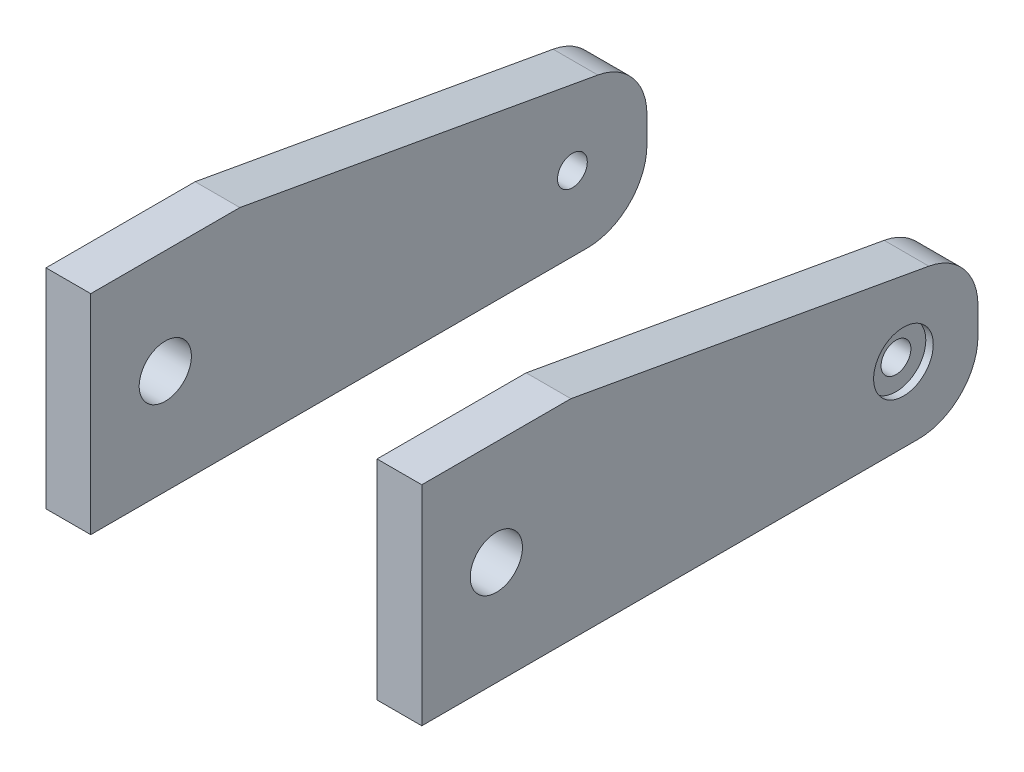
SolidWorks part; units mm, degrees
ref_plane "Front Plane" through (0, 0, 0) normal (0, 0, 1) x (1, 0, 0)
ref_plane "Top Plane" through (0, 0, 0) normal (0, 1, 0) x (1, 0, 0)
ref_plane "Right Plane" through (0, 0, 0) normal (1, 0, 0) x (0, 0, -1)
sketch "Sketch2" plane through (9.6, 0, 0) normal (1, 0, 0) x (0, 0, -1)
  line L0 (-22.3234, -11) -> (0.9766, -11)
  line L1 (4.9766, -7) -> (4.9766, -5.2432)
  line L2 (1.6828, -1.306) -> (-22.3234, 3)
  line L3 (-22.3234, 3) -> (-22.3234, -11) construction
  line L4 (-9.6234, -7.3) -> (-9.6234, 0) construction
  line L5 (-22.3234, -11) -> (-32.3234, -11)
  line L6 (-32.3234, -11) -> (-32.3234, 3)
  line L7 (-32.3234, 3) -> (-22.3234, 3)
  line L8 (-32.3234, -11) -> (-22.3234, 3) construction
  circle A0 centre (-0.0234, -6) radius 1 construction
  circle A1 centre (-0.0234, -6) radius 1
  arc A2 (0.9766, -11) -> (4.9766, -7) centre (0.9766, -7) ccw
  arc A3 (4.9766, -5.2432) -> (1.6828, -1.306) centre (0.9766, -5.2432) ccw
  circle A4 centre (-27.3234, -4) radius 1.75
  point P13 (-0.0234, -1)
  point P17 (0, 0)
  dimension "D1" = 4
  dimension "D8" = 3.5
  dimension "D2" = 4
  dimension "D3" = 4
  dimension "D4" = 4
  dimension "D5" = 12.7
  dimension "D6" = 14
  dimension "D7" = 10
extrude "Boss-Extrude1" add sketch "Sketch2" along normal blind 3
sketch "Sketch3" plane through (12.6, 0, 0) normal (1, 0, 0) x (0, 0, -1)
  circle A0 centre (-0.0234, -6) radius 1 construction
  circle A1 centre (-0.0234, -6) radius 1 construction
  circle A2 centre (-0.0234, -6) radius 2
  dimension "D1" = 4
extrude "Cut-Extrude1" cut sketch "Sketch3" against normal blind 0.5
mirror "Mirror4" about plane through (0, 0, 0) normal (1, 0, 0) of bodies 105 101
